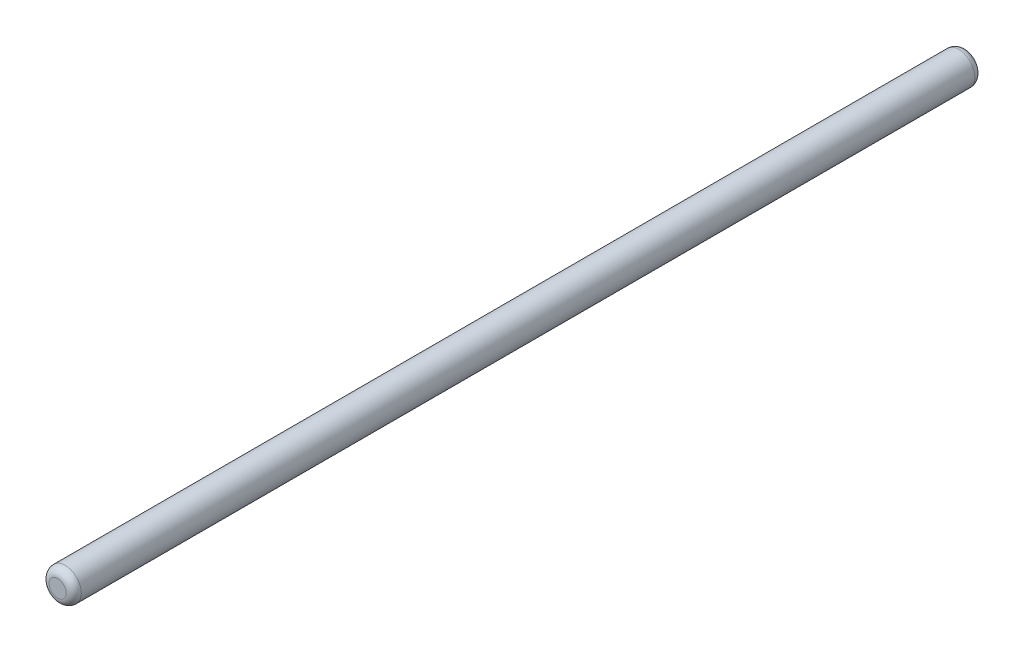
SolidWorks part; units mm, degrees
ref_plane "Front Plane" through (0, 0, 0) normal (0, 0, 1) x (1, 0, 0)
ref_plane "Top Plane" through (0, 0, 0) normal (0, 1, 0) x (1, 0, 0)
ref_plane "Right Plane" through (0, 0, 0) normal (1, 0, 0) x (0, 0, -1)
sketch "Sketch1" plane through (0, 0, 0) normal (0, 0, 1) x (1, 0, 0)
  circle A0 centre (0, 0) radius 4.25
  dimension "D1" = 8.5
extrude "Boss-Extrude1" add sketch "Sketch1" along normal mid plane 240
fillet "Fillet1" radius 2 2 edges at (4.25, 0, -120) (4.25, 0, 120)
